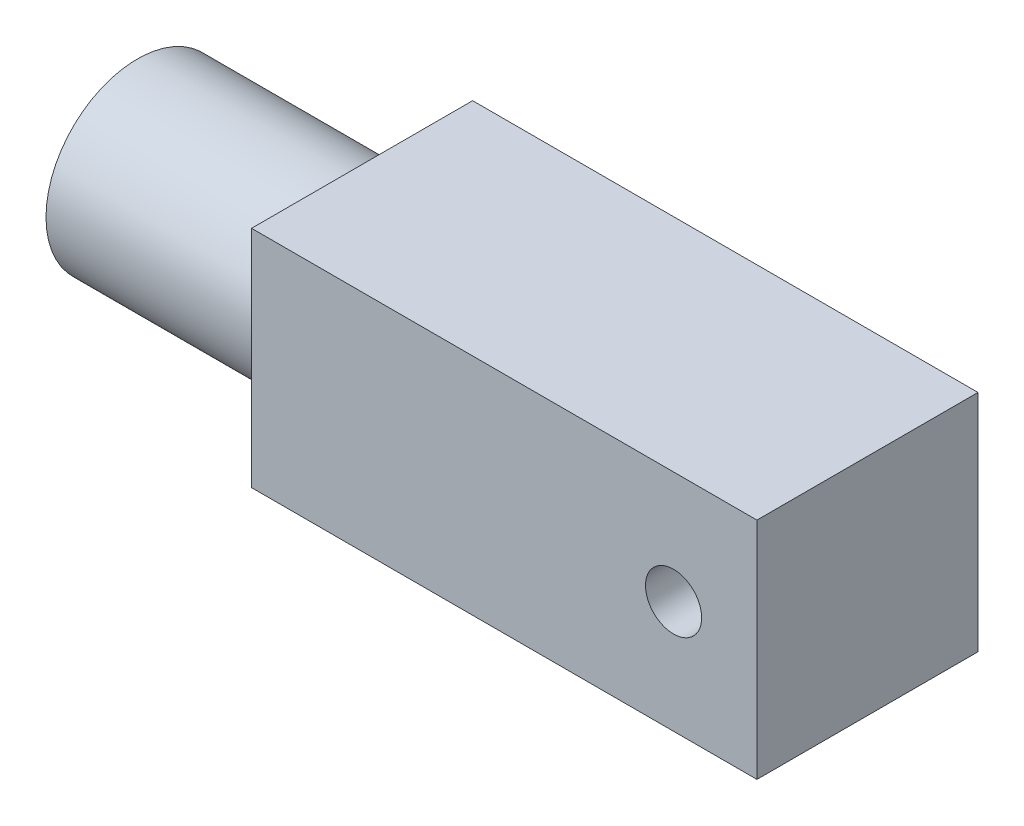
SolidWorks part; units mm, degrees
ref_plane "Front Plane" through (0, 0, 0) normal (0, 0, 1) x (1, 0, 0)
ref_plane "Top Plane" through (0, 0, 0) normal (0, 1, 0) x (1, 0, 0)
ref_plane "Right Plane" through (0, 0, 0) normal (1, 0, 0) x (0, 0, -1)
sketch "Sketch1" plane through (0, 0, 1.2852) normal (0, 1, 0) x (1, 0, 0)
  line L1 (-28.2487, 0) -> (17.4713, 0)
  line L2 (-28.2487, 0) -> (-28.2487, 20)
  line L3 (-28.2487, 20) -> (17.4713, 20)
  line L4 (17.4713, 0) -> (17.4713, 20)
  dimension "D1" = 20
  dimension "D2" = 45.72
extrude "Boss-Extrude1" add sketch "Sketch1" along normal blind 20.32
sketch "Sketch2" plane through (-28.2487, 0, 1.2852) normal (-1, 0, 0) x (0, 0, 1)
  circle A0 centre (-10, 10.16) radius 8.2761
extrude "Boss-Extrude2" add sketch "Sketch2" along normal blind 20.32 contours A0
sketch "Sketch4" plane through (0, 0, 1.2852) normal (0, 0, 1) x (1, 0, 0)
  circle A0 centre (9.9287, 10.16) radius 2.54
  dimension "D1" = 5.08
extrude "Cut-Extrude1" cut sketch "Sketch4" against normal blind 19.05
sketch "Sketch5" plane through (0, 0, 1.2852) normal (0, -1, 0) x (1, 0, 0)
  text T0 "Motor"
